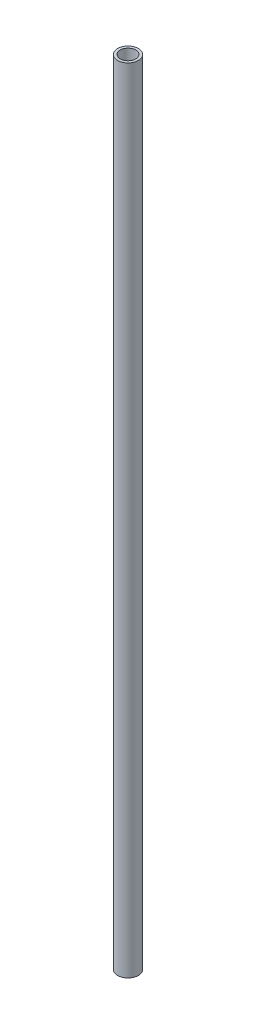
SolidWorks part; units mm, degrees
material "Copper"
ref_plane "Front Plane" through (0, 0, 0) normal (0, 0, 1) x (1, 0, 0)
ref_plane "Top Plane" through (0, 0, 0) normal (0, 1, 0) x (1, 0, 0)
ref_plane "Right Plane" through (0, 0, 0) normal (1, 0, 0) x (0, 0, -1)
sketch "Sketch1" plane through (0, 0, 0) normal (0, 1, 0) x (1, 0, 0)
  circle A0 centre (0, 0) radius 1.5
  circle A1 centre (0, 0) radius 2
  dimension "D1" = 4
  dimension "D2" = 3
extrude "Boss-Extrude1" add sketch "Sketch1" along normal mid plane 153
